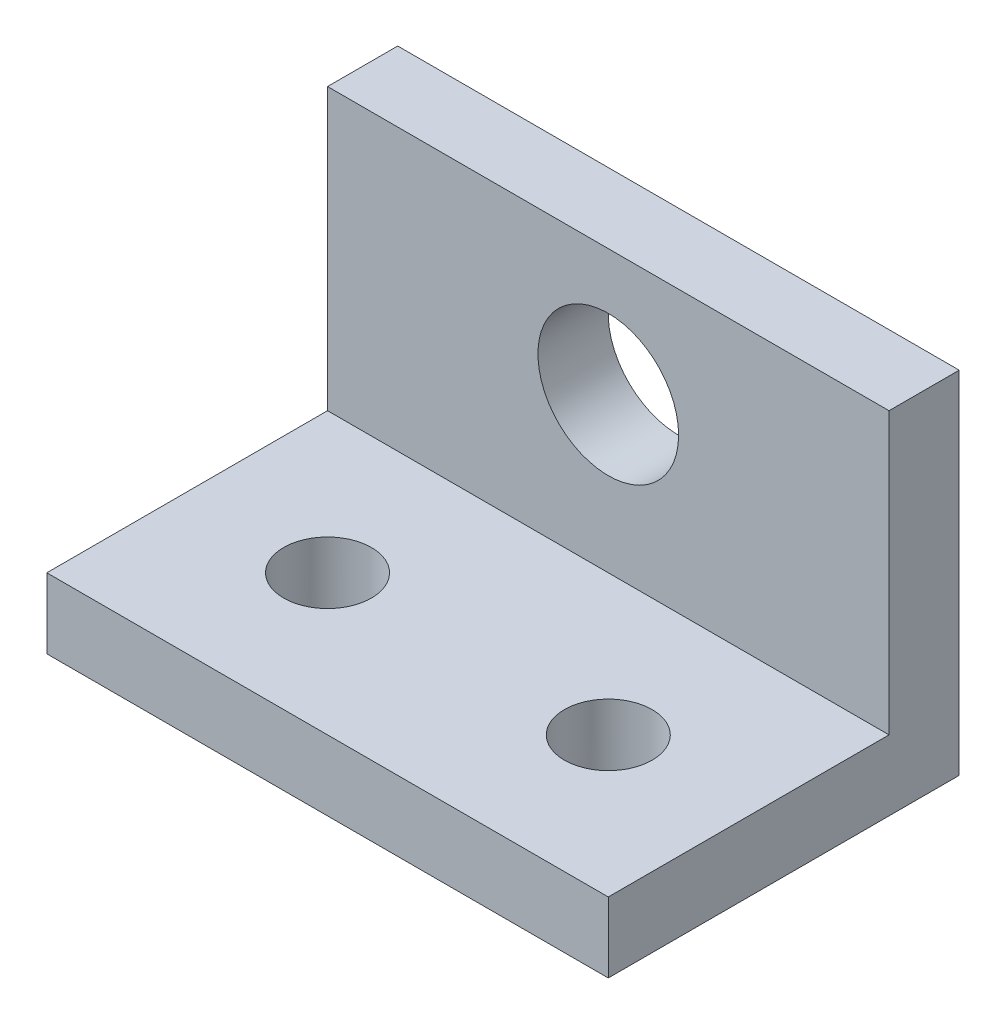
SolidWorks part; units mm, degrees
ref_plane "Front Plane" through (0, 0, 0) normal (0, 0, 1) x (1, 0, 0)
ref_plane "Top Plane" through (0, 0, 0) normal (0, 1, 0) x (1, 0, 0)
ref_plane "Right Plane" through (0, 0, 0) normal (1, 0, 0) x (0, 0, -1)
sketch "Sketch1" plane through (0, 0, 0) normal (1, 0, 0) x (0, 0, -1)
  line L1 (0, 0) -> (-6.35, 0)
  line L2 (0, 0) -> (0, 31.75)
  line L3 (0, 31.75) -> (-6.35, 31.75)
  line L4 (-6.35, 0) -> (-6.35, 31.75)
  line L5 (-6.35, 0) -> (-31.75, 0)
  line L6 (-6.35, 0) -> (-6.35, 6.35)
  line L7 (-6.35, 6.35) -> (-31.75, 6.35)
  line L8 (-31.75, 0) -> (-31.75, 6.35)
  dimension "D1" = 6.35
  dimension "D2" = 6.35
  dimension "D3" = 31.75
  dimension "D4" = 31.75
extrude "Boss-Extrude1" add sketch "Sketch1" along normal blind 50.8 contours L8 L5 L4 L7 | L4 L1 L2 L3
sketch "Sketch2" plane through (0, 0, 6.35) normal (0, 0, 1) x (1, 0, 0)
  line L0 (0, 20.32) -> (50.8, 20.32) construction
  line L1 (0, 6.35) -> (0, 31.75) construction
  line L2 (50.8, 6.35) -> (50.8, 31.75) construction
  line L3 (50.8, 6.35) -> (0, 6.35) construction
  circle A0 centre (25.4, 20.32) radius 6.3627
  dimension "D1" = 12.7254
  dimension "D2" = 13.97
extrude "Cut-Extrude1" cut sketch "Sketch2" against normal up to next
sketch "Sketch3" plane through (0, 6.35, 0) normal (0, 1, 0) x (1, 0, 0)
  line L0 (0, -19.05) -> (50.8, -19.05) construction
  line L1 (0, -6.35) -> (0, -31.75) construction
  line L2 (50.8, -6.35) -> (50.8, -31.75) construction
  line L3 (50.8, -31.75) -> (50.8, -6.35) construction
  circle A0 centre (12.7, -19.05) radius 3.9688
  circle A1 centre (38.1, -19.05) radius 3.9687
  dimension "D1" = 7.9375
  dimension "D2" = 7.9375
  dimension "D3" = 12.7
  dimension "D4" = 12.7
extrude "Cut-Extrude2" cut sketch "Sketch3" against normal up to next
